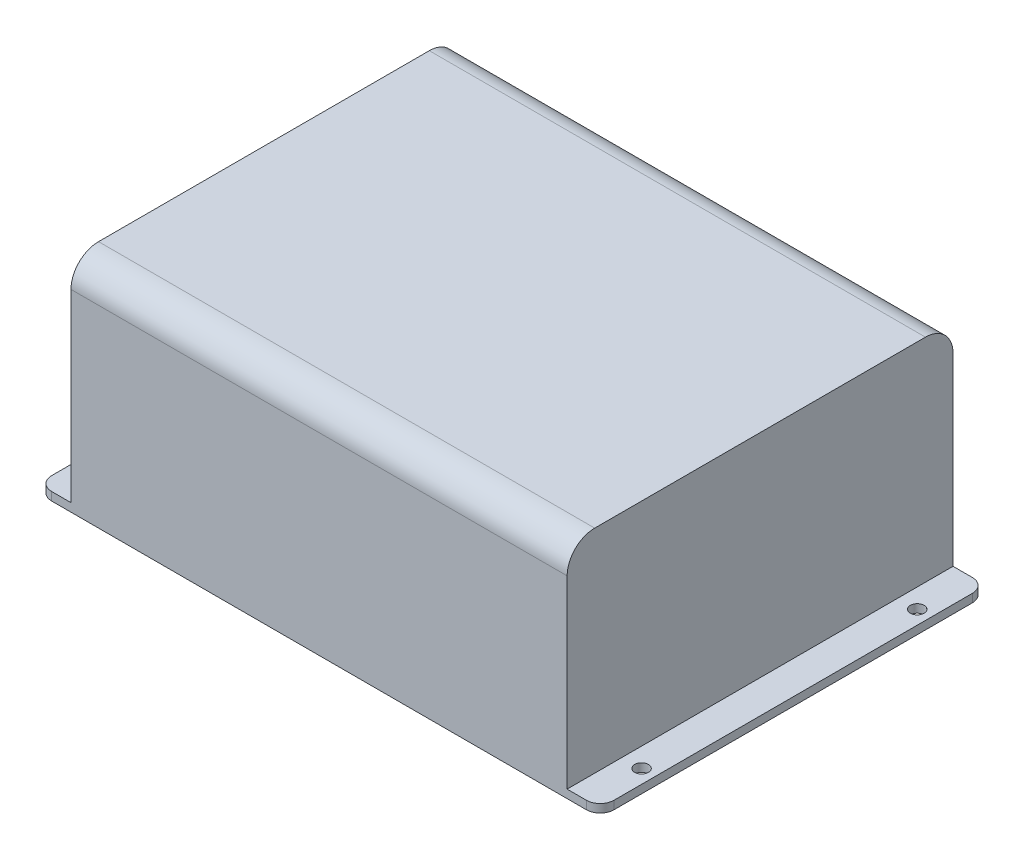
SolidWorks part; units mm, degrees
ref_plane "Alzado" through (0, 0, 0) normal (0, 0, 1) x (1, 0, 0)
ref_plane "Planta" through (0, 0, 0) normal (0, 1, 0) x (1, 0, 0)
ref_plane "Vista lateral" through (0, 0, 0) normal (1, 0, 0) x (0, 0, -1)
sketch "Croquis1" plane through (0, 0, 0) normal (0, 1, 0) x (1, 0, 0)
  line L1 (-90, 70) -> (90, 70)
  line L2 (-90, 70) -> (-90, -70)
  line L3 (-90, -70) -> (90, -70)
  line L4 (90, 70) -> (90, -70)
  line L5 (-90, 70) -> (90, -70) construction
  line L6 (-90, -70) -> (90, 70) construction
  point P0 (0, 0)
  dimension "D1" = 180
  dimension "D2" = 140
extrude "Saliente-Extruir1" add sketch "Croquis1" along normal blind 80
sketch "Croquis2" plane through (0, 0, 0) normal (0, -1, 0) x (1, 0, 0)
  line L0 (90, -70) -> (-90, -70) construction
  line L1 (90, 70) -> (102, 70)
  line L2 (90, 70) -> (90, -70)
  line L3 (90, -70) -> (102, -70)
  line L4 (102, 70) -> (102, -70)
  line L5 (90, 70) -> (102, -70) construction
  line L6 (90, -70) -> (102, 70) construction
  point P4 (96, 0)
  dimension "D1" = 12
extrude "Saliente-Extruir2" add sketch "Croquis2" against normal blind 3
fillet "Redondeo1" radius 5 2 edges at (102, 1.5, -70) (102, 1.5, 70)
sketch "Croquis3" plane through (0, 3, 0) normal (0, 1, 0) x (1, 0, 0)
  line L0 (97, -90) -> (97, 49910) construction
  line L1 (0, 0) -> (50000, 0) construction
  circle A0 centre (97, 50) radius 2.5
  circle A2 centre (97, -50) radius 2.5
  dimension "D1" = 5
  dimension "D2" = 100
extrude "Cortar-Extruir1" cut sketch "Croquis3" against normal through all
mirror "Simetría1" about plane through (0, 0, 0) normal (1, 0, 0) of "Redondeo1", "Cortar-Extruir1", "Saliente-Extruir2"
fillet "Redondeo2" radius 10 2 edges at (0, 80, 70) (0, 80, -70)
